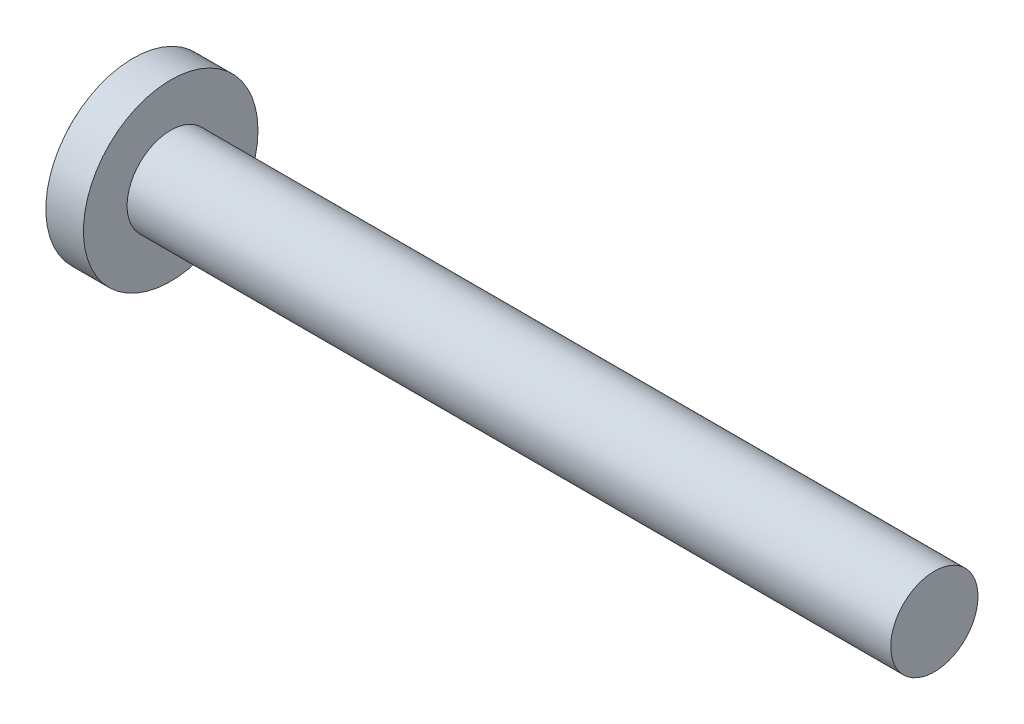
SolidWorks part; units mm, degrees
ref_plane "Front" through (0, 0, 0) normal (0, 0, 1) x (1, 0, 0)
ref_plane "Top" through (0, 0, 0) normal (0, 1, 0) x (1, 0, 0)
ref_plane "Right" through (0, 0, 0) normal (1, 0, 0) x (0, 0, -1)
sketch "Sketch1" plane through (0, 0, 0) normal (0, 0, 1) x (1, 0, 0)
  line L0 (38.1, 2) -> (4.5, 2)
  line L1 (3.1, 2.35) -> (3.1, 4)
  line L2 (3.1, 4) -> (1.3765, 4)
  line L3 (4.5, 2) -> (3.3865, 2.0503) construction
  line L4 (38.1, 2) -> (38.1, 0)
  line L5 (4.5158, 0) -> (-13.5157, 0) construction
  line L6 (38.1, 0) -> (0, 0)
  line L7 (4.5, 2) -> (3.1, 2)
  line L8 (3.1, 2) -> (3.1, 2.35)
  arc A0 (1.3765, 4) -> (0, 0) centre (6.5, 0) ccw
  arc A1 (3.1, 2.35) -> (3.3865, 2.0503) centre (3.4, 2.35) ccw construction
  dimension "r" = 0.3
  dimension "r1" = 6.5
  dimension "d" = 4
  dimension "dk" = 8
  dimension "l" = 35
  dimension "a" = 1.4
  dimension "da" = 4.7
  dimension "k" = 3.1
revolve "Base" add sketch "Sketch1" angle 360 about L5
cosmetic thread "ThreadCosmetic1" [suppressed] parameters "bb"=14, "THD_MINOR"=3.242
sketch "Sketch6" plane through (0, 0, 0) normal (1, 0, 0) x (0, 0, -1)
  line L0 (-1.9271, 0) -> (2.0512, 0) construction
  line L1 (0, 1.8651) -> (0, -2.0207) construction
  line L2 (0.44, 0.44) -> (0.44, 2.2)
  line L3 (0.44, 2.2) -> (-0.44, 2.2)
  line L4 (-0.44, 0.44) -> (-0.44, 2.2)
  line L5 (0.44, 0.44) -> (2.2, 0.44)
  line L6 (2.2, 0.44) -> (2.2, -0.44)
  line L7 (-2.2, 0.44) -> (-2.2, -0.44)
  line L8 (-0.44, 0.44) -> (-2.2, 0.44)
  line L9 (-0.44, -0.44) -> (-2.2, -0.44)
  line L10 (0.44, -0.44) -> (2.2, -0.44)
  line L11 (-0.44, -0.44) -> (-0.44, -2.2)
  line L12 (0.44, -2.2) -> (-0.44, -2.2)
  line L13 (0.44, -0.44) -> (0.44, -2.2)
  point P16 (-2.2, 0)
  point P17 (2.2, 0)
extrude "CrossRecess" cut sketch "Sketch6" along normal blind 2.17
fillet "Fillet5" radius 0.3 4 edges at (1.0999, -0.44, 0.44) (1.0999, -0.44, -0.44) (1.0999, 0.44, 0.44) (1.0999, 0.44, -0.44)
draft "Draft1" type of draft neutral plane draft angle 30 neutral plane "Right" faces to draft 4 face at (1.2808, -2.2, 0) face at (1.2808, 0, -2.2) face at (1.2808, 0, 2.2) face at (1.2808, 2.2, 0) neutral plane through (0, 0, 0) neutral plane normal (1, 0, 0) reverse direction yes parameters "D1"=30
sketch "Sketch7" plane through (0, 0, 0) normal (1, 0, 0) x (0, 0, -1)
  line L0 (-2.0126, 0) -> (1.9757, 0) construction
  line L1 (0, 1.9314) -> (0, -2.0126) construction
  line L2 (0, 0) -> (1.5555, 1.5555) construction
  line L3 (0, 0.6575) -> (1.5556, 1.5556)
  line L4 (-1.5402, 1.5402) -> (0, 0) construction
  line L5 (0.6575, 0) -> (1.5556, 1.5556)
  line L6 (0, -0.6575) -> (1.5556, -1.5556)
  line L7 (0.6575, 0) -> (1.5556, -1.5556)
  line L8 (-0.6575, 0) -> (-1.5556, -1.5556)
  line L9 (0, -0.6575) -> (-1.5556, -1.5556)
  line L10 (-0.6575, 0) -> (-1.5556, 1.5556)
  line L11 (0, 0.6575) -> (-1.5556, 1.5556)
  dimension "D3" = 15
  dimension "m" = 4.4
extrude "Cut-Extrude3" [suppressed] cut sketch "Sketch7" along normal blind 40.2 draft 9
sketch "Sketch8" plane through (0, 0, 0) normal (0, 0, 1) x (1, 0, 0)
  line L0 (0.1, 2) -> (-1.65, 1.621)
  line L1 (-1.65, 1.621) -> (3.1, 1.621)
  line L2 (38.1, -2) -> (38.1, 2) construction
  line L3 (3.1, -4) -> (3.1, 4) construction
  line L6 (3.1, 1.621) -> (3.1, 4)
  line L7 (3.1, 4) -> (0.1, 4)
  line L8 (0.1, 4) -> (0.1, 2)
  line L9 (73.4853, 0) -> (63.9694, 0) construction
  dimension "x" = 1.75
  dimension "d" = 4
  dimension "THD_MINOR" = 3.242
  dimension "b" = 38
sketch "Sketch9" plane through (0, 0, 0) normal (0, 0, 1) x (1, 0, 0)
  line L0 (38.1, 1.6718) -> (38.2895, 2)
  line L1 (38.2895, 2) -> (38.2895, 2.379)
  line L2 (38.2895, 2.379) -> (37.9105, 2.379)
  line L3 (37.9105, 2.379) -> (37.9105, 2)
  line L4 (37.9105, 2) -> (38.1, 1.6718)
  line L5 (38.1, -2) -> (38.1, 2) construction
  line L6 (0, 0) -> (76.7811, 0) construction
  dimension "D1" = 4
  dimension "D2" = 0.379
revolve "Cut-Revolve10" [suppressed] cut sketch "Sketch9" angle 360 about L6
pattern_linear "LPattern10" [suppressed] count 77 spacing 0.4548 along (1, 0, 0)
equation "\"D1@Sketch6\" = \"m@Sketch6\" / 5"
equation "\"D1@CrossRecess\" = 0.7*\"k@Sketch1\""
equation "\"D1@Sketch9\" = \"d@Sketch1\" "
equation "\"D2@Sketch9\" =  ( \"d@Sketch1\" - \"THD_MINOR@ThreadCosmetic1\" )  / 2"
equation "\"D3@LPattern10\" =\"D2@Sketch9\" * 1.2"
equation "\"D1@LPattern10\" = \"bb@ThreadCosmetic1\" / \"D3@LPattern10\" "
